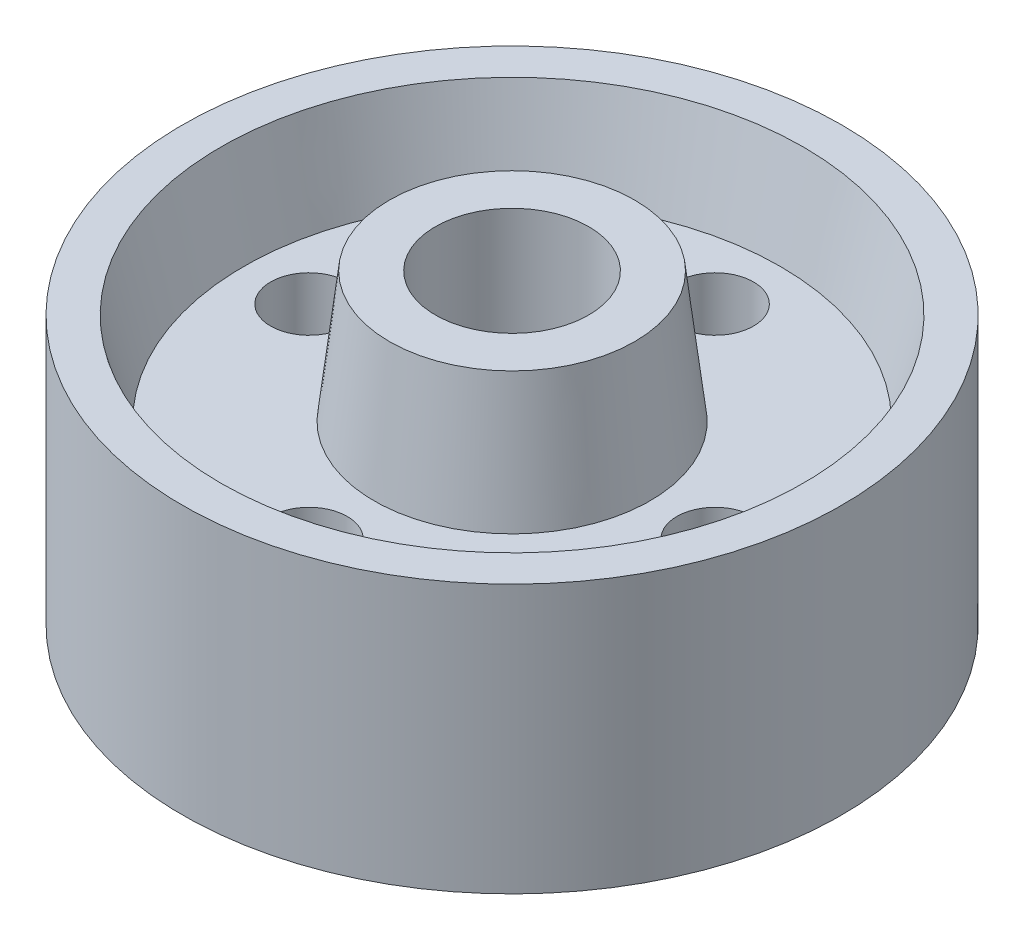
SolidWorks part; units mm, degrees
ref_plane "Front Plane" through (0, 0, 0) normal (1, 0, 0) x (0, 1, 0)
ref_plane "Top Plane" through (0, 0, 0) normal (0, 0, 1) x (0, 1, 0)
ref_plane "Right Plane" through (0, 0, 0) normal (0, 1, 0) x (-1, 0, 0)
sketch "Sketch1" plane through (0, 0, 0) normal (0, 0, 1) x (0, 1, 0)
  line L0 (0, 0) -> (35, 0)
  line L1 (0, 43) -> (35, 43)
  line L3 (0, 43) -> (0, 0) construction
  line L6 (12, 35) -> (12, 18)
  line L7 (0, 43) -> (0, 38)
  line L8 (23, 35) -> (23, 18)
  line L9 (35, 43) -> (35, 38)
  line L10 (0, 38) -> (12, 35)
  line L11 (23, 35) -> (35, 38)
  line L12 (-5, 16) -> (12, 18)
  line L14 (12, 43) -> (12, 0) construction
  line L15 (23, 43) -> (23, 0) construction
  line L17 (17.5, 6.5041) -> (17.5, 43) construction
  line L19 (40, 16) -> (23, 18)
  line L21 (-5, 0) -> (0, 0)
  line L22 (35, 0) -> (40, 0)
  line L24 (-5, 16) -> (-5, 0)
  line L25 (40, 16) -> (40, 0)
  point P7 (0, 0)
  point P8 (0, 0)
  dimension "D1" = 43
  dimension "D2" = 35
  dimension "D3" = 35
  dimension "D4" = 12.3693
  dimension "D5" = 38
  dimension "D6" = 16
  dimension "D7" = 18
  dimension "D8" = 12
  dimension "D10" = 17
  dimension "D11" = 45
  dimension "D12" = 8
  dimension "D13" = 12.3693
  dimension "D9" = 11
revolve "Revolve1" add sketch "Sketch1" angle 360 about L0
sketch "Sketch2" plane through (0, -5, 0) normal (0, -1, 0) x (1, 0, 0)
  circle A0 centre (0, 0) radius 10
  dimension "D1" = 20
extrude "Cut-Extrude1" cut sketch "Sketch2" against normal through all
sketch "Sketch3" plane through (0, 23, 0) normal (0, 1, 0) x (-1, 0, 0)
  circle A0 centre (0, 0) radius 26.5 construction
  circle A1 centre (0, 26.5) radius 5
  circle A2 centre (26.5, 0) radius 5
  circle A3 centre (0, -26.5) radius 5
  circle A4 centre (-26.5, 0) radius 5
  point P5 (-30.6222, -1.6669)
  point P6 (0, 0)
  point P7 (0, 0)
  point P14 (0, 0)
  dimension "D1" = 53
  dimension "D2" = 10
  dimension "D3" = 4
extrude "Cut-Extrude2" cut sketch "Sketch3" against normal through all
